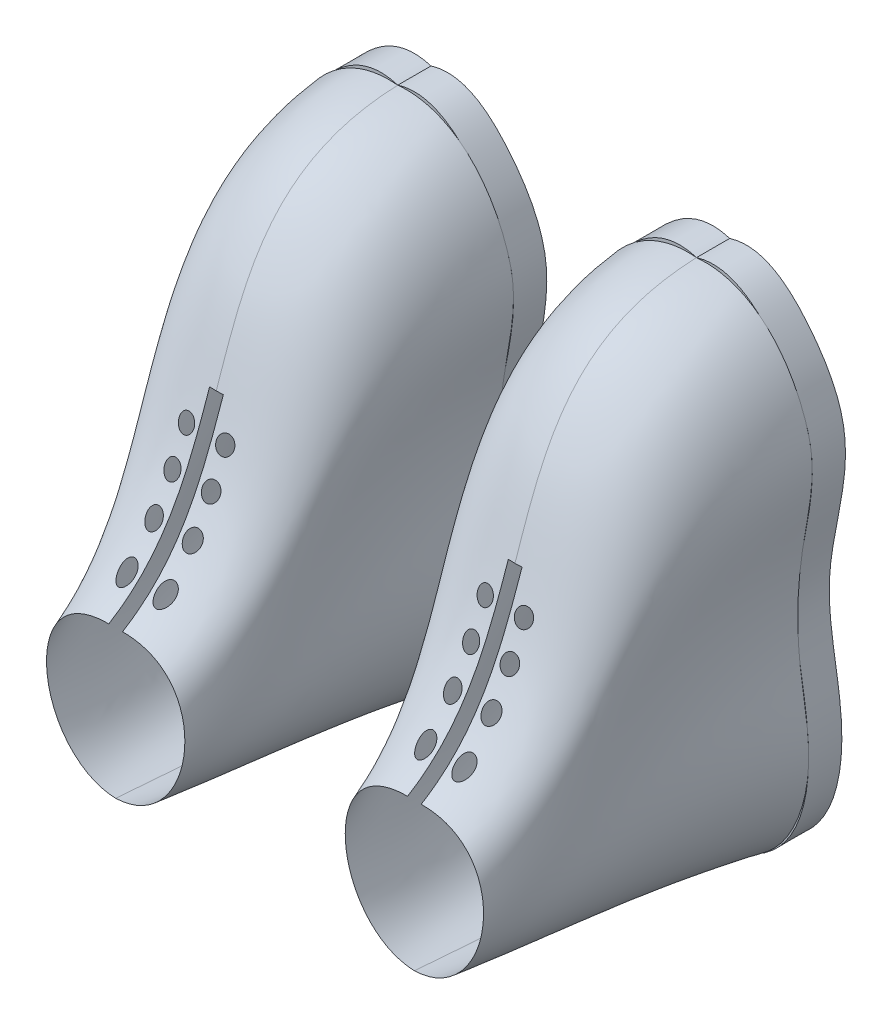
SolidWorks part; units mm, degrees
ref_plane "Front Plane" through (0, 0, 0) normal (0, 0, 1) x (1, 0, 0)
ref_plane "Top Plane" through (0, 0, 0) normal (0, 1, 0) x (1, 0, 0)
ref_plane "Right Plane" through (0, 0, 0) normal (1, 0, 0) x (0, 0, -1)
sketch "Sketch2" plane through (0, 0, 0) normal (0, 0, 1) x (1, 0, 0)
  spline S0 degree 3 poles (0, 99.1833) (9.9401, 102.2623) (24.1226, 90.4641) (40.3345, 61.9432) (25.18, 26.4363) (39.0472, -17.7172) (27.2802, -52.0991) (0, -50.8167) knots 0 0 0 0 0.146529 0.268877 0.50326 0.69401 1 1 1 1
  spline S1 degree 3 poles (0, 99.1833) (-9.9401, 102.2623) (-24.1226, 90.4641) (-40.3345, 61.9432) (-25.18, 26.4363) (-39.0472, -17.7172) (-27.2802, -52.0991) (0, -50.8167) knots 0 0 0 0 0.146529 0.268877 0.50326 0.69401 1 1 1 1
extrude "Boss-Extrude1" add sketch "Sketch2" along normal blind 10
ref_plane "Plane1" through (0, 0, 10) normal (0, 0, 1) x (1, 0, 0)
sketch "Sketch3" plane through (0, 0, 10) normal (0, 0, 1) x (1, 0, 0)
  spline S0 degree 3 poles (0, 99.1833) (-17.1467, 100.6984) (-29.7135, 85.2596) (-36.3506, 60.1853) (-30.961, 39.1158) (-29.5324, 10.3923) (-37.1307, -19.0046) (-24.8521, -49.0317) (-5.9362, -51.0729) (0, -50.8167) knots 0 0 0 0 0.244049 0.265991 0.413933 0.57758 0.721998 0.901928 1 1 1 1
  spline S1 degree 3 poles (0, 99.1833) (-9.9401, 102.2623) (-24.1226, 90.4641) (-40.3345, 61.9432) (-25.18, 26.4363) (-39.0472, -17.7172) (-27.2802, -52.0991) (0, -50.8167) knots 0 0 0 0 0.146529 0.268877 0.50326 0.69401 1 1 1 1 construction
  spline S2 degree 3 poles (0, 99.1833) (17.1467, 100.6984) (29.7135, 85.2596) (36.3506, 60.1853) (30.961, 39.1158) (29.5324, 10.3923) (37.1307, -19.0046) (24.8521, -49.0317) (5.9362, -51.0729) (0, -50.8167) knots 0 0 0 0 0.244049 0.265991 0.413933 0.57758 0.721998 0.901928 1 1 1 1
ref_plane "Plane2" through (0, 0, 95) normal (0, 0, 1) x (1, 0, 0)
sketch "Sketch4" plane through (0, 0, 95) normal (0, 0, 1) x (1, 0, 0)
  spline S0 degree 3 poles (0, 0) (-18.9282, 1.3946) (-26.9108, -26.2332) (-9.3887, -44.1012) (0, -44.4111) knots 0 0 0 0 0.600416 1 1 1 1
  spline S1 degree 3 poles (0, 0) (18.9282, 1.3946) (26.9108, -26.2332) (9.3887, -44.1012) (0, -44.4111) knots 0 0 0 0 0.600416 1 1 1 1
sketch3d "3DSketch8"
  spline S0 degree 1 poles (0, -50.8167, 10) (0, -44.4111, 95) knots 0 0 1 1
  spline S1 degree 1 poles (9.8039, -41.2392, 95) (17.9339, -47.4274, 10) knots 0 0 1 1
  spline S2 degree 1 poles (-9.8039, -41.2392, 95) (-17.9339, -47.4274, 10) knots 0 0 1 1
ref_plane "Plane3" through (0, 0, 105) normal (0, 0, 1) x (1, 0, 0)
sketch "Sketch5" plane through (0, 0, 105) normal (0, 0, 1) x (1, 0, 0)
  line L1 (-2.0671, 46.7507) -> (2.0671, 46.7507)
  line L2 (-2.0671, 46.7507) -> (-2.0671, -1.0879)
  line L3 (-2.0671, -1.0879) -> (2.0671, -1.0879)
  line L4 (2.0671, 46.7507) -> (2.0671, -1.0879)
  line L5 (-2.0671, 46.7507) -> (2.0671, -1.0879) construction
  line L6 (-2.0671, -1.0879) -> (2.0671, 46.7507) construction
  circle A0 centre (5.8297, 7.1092) radius 2.5
  circle A1 centre (5.8297, 17.1092) radius 2.5
  circle A2 centre (5.8297, 27.1092) radius 2.5
  circle A3 centre (5.8297, 37.1092) radius 2.5
  circle A4 centre (-5.8297, 17.1092) radius 2.5
  circle A5 centre (-5.8297, 27.1092) radius 2.5
  circle A6 centre (-5.8297, 37.1092) radius 2.5
  circle A7 centre (-5.8297, 7.1092) radius 2.5
  point P0 (0, 22.8314)
  point P22 (0, 0)
  dimension "D1" = 4
sketch "Sketch6" plane through (0, 0, 105) normal (0, 0, 1) x (1, 0, 0)
sketch3d "3DSketch11"
  spline S0 degree 3 poles (0, 0, 95) (0, 25.5742, 52.3373) (0, 96.6986, 74.4677) (0, 99.1833, 10) knots 0 0 0 0 1 1 1 1
  spline S1 degree 3 poles (0, 0, 95) (-18.9282, 1.3946, 95) (-26.9108, -26.2332, 95) (-9.3887, -44.1012, 95) (0, -44.4111, 95) knots 0 0 0 0 0.600416 1 1 1 1 construction
surface "Surface-Loft3"
surface "Surface-Trim2"
ref_plane "Plane4" through (45, 0, 0) normal (1, 0, 0) x (0, 0, -1)
mirror "Mirror2" about plane through (45, 0, 0) normal (1, 0, 0) of bodies 106 101
